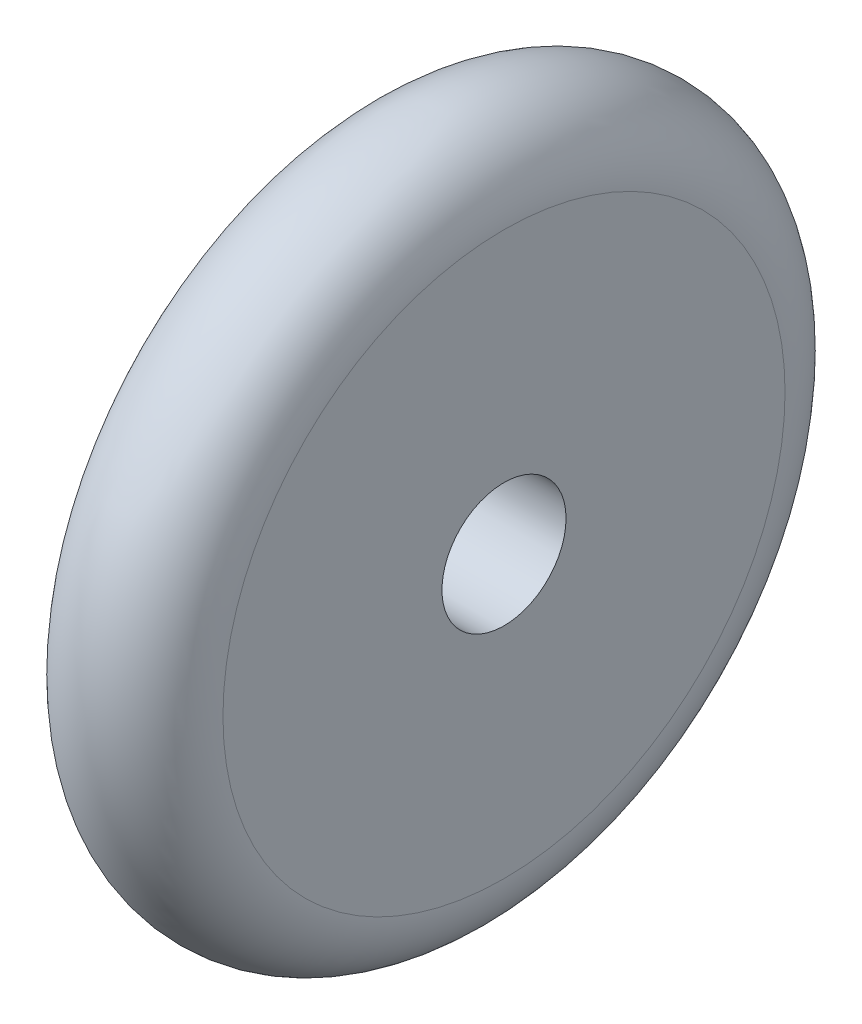
SolidWorks part; units mm, degrees
ref_plane "Front Plane" through (0, 0, 0) normal (0, 0, 1) x (1, 0, 0)
ref_plane "Top Plane" through (0, 0, 0) normal (0, 1, 0) x (1, 0, 0)
ref_plane "Right Plane" through (0, 0, 0) normal (1, 0, 0) x (0, 0, -1)
sketch "Sketch1" plane through (0, 0, 0) normal (0, 0, 1) x (1, 0, 0)
  line L0 (4, 0) -> (4, -1.7) construction
  line L1 (0, 0) -> (4, 0)
  line L2 (0, 0) -> (0, 6)
  line L3 (0, 6) -> (4, 6)
  line L4 (4, 0) -> (4, 6)
  line L5 (4, -1.7) -> (-0.2518, -1.7) construction
  arc A0 (0, 6) -> (4, 6) centre (2, 6) cw
  dimension "D1" = 6
  dimension "D2" = 1.7
  dimension "D3" = 4
revolve "Revolve1" add sketch "Sketch1" angle 360 about L5
